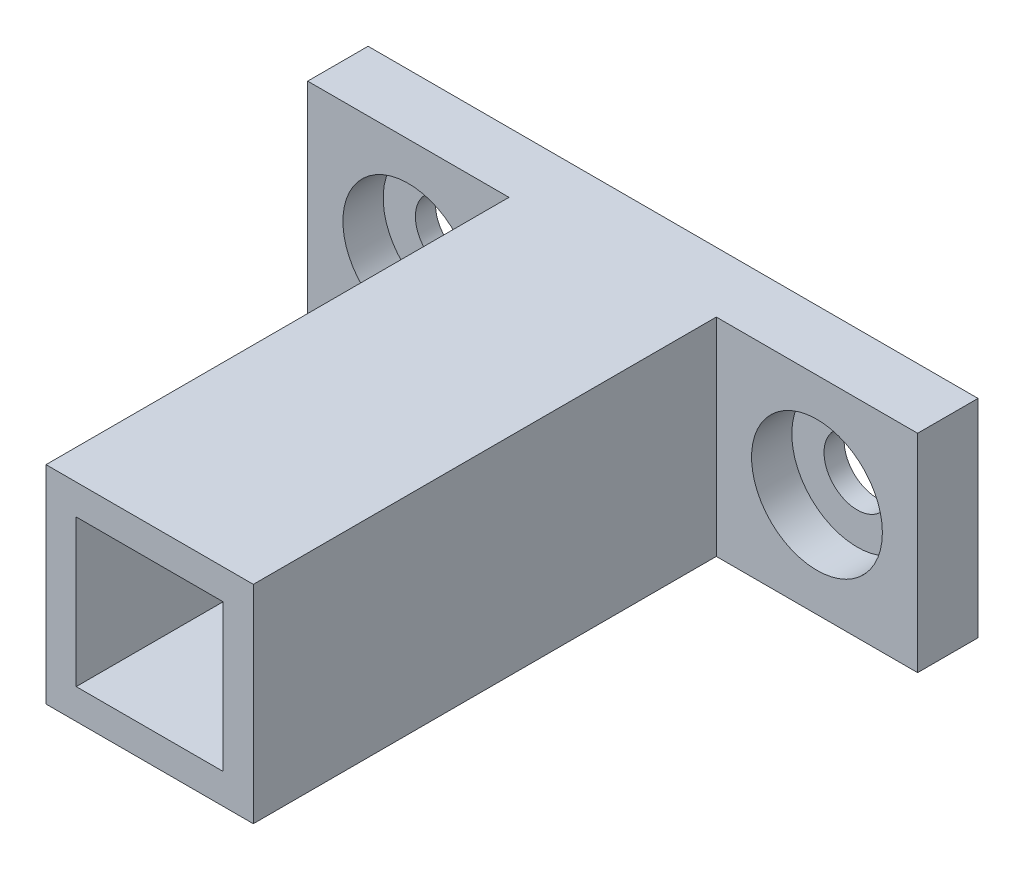
SolidWorks part; units mm, degrees
ref_plane "Alzado" through (0, 0, 0) normal (0, 0, 1) x (1, 0, 0)
ref_plane "Planta" through (0, 0, 0) normal (0, 1, 0) x (1, 0, 0)
ref_plane "Vista lateral" through (0, 0, 0) normal (1, 0, 0) x (0, 0, -1)
sketch "Croquis1" plane through (0, 0, 0) normal (0, 0, 1) x (1, 0, 0)
  line L8 (-60.1239, 65.6327) -> (-60.1239, 58.3327) construction
  line L9 (-60.1239, 65.6327) -> (-52.8239, 65.6327) construction
  line L10 (-52.8239, 65.6327) -> (-52.8239, 58.3327) construction
  line L11 (-60.1239, 58.3327) -> (-52.8239, 58.3327) construction
  line L24 (-60.1239, 65.6327) -> (-60.1239, 58.3327)
  line L25 (-60.1239, 65.6327) -> (-52.8239, 65.6327)
  line L26 (-52.8239, 65.6327) -> (-52.8239, 58.3327)
  line L27 (-60.1239, 58.3327) -> (-52.8239, 58.3327)
  line L32 (-61.6239, 67.1327) -> (-61.6239, 56.8327)
  line L33 (-61.6239, 56.8327) -> (-51.3239, 56.8327)
  line L34 (-51.3239, 67.1327) -> (-51.3239, 56.8327)
  line L35 (-61.6239, 67.1327) -> (-51.3239, 67.1327)
  dimension "D1" = 1.5
extrude "Saliente-Extruir1" add sketch "Croquis1" along normal blind 26
sketch "Croquis2" plane through (0, 0, 0) normal (0, 0, 1) x (1, 0, 0)
  line L14 (-51.3239, 67.1327) -> (-61.6239, 67.1327) construction
  line L15 (-51.3239, 67.1327) -> (-41.3239, 67.1327)
  line L16 (-51.3239, 67.1327) -> (-51.3239, 56.8327)
  line L17 (-51.3239, 56.8327) -> (-41.3239, 56.8327)
  line L18 (-41.3239, 67.1327) -> (-41.3239, 56.8327)
  line L19 (-61.6239, 56.8327) -> (-51.3239, 56.8327) construction
  line L20 (-61.6239, 67.1327) -> (-71.6239, 67.1327)
  line L21 (-61.6239, 67.1327) -> (-61.6239, 56.8327)
  line L22 (-61.6239, 56.8327) -> (-71.6239, 56.8327)
  line L23 (-71.6239, 67.1327) -> (-71.6239, 56.8327)
  line L24 (-51.3239, 56.8327) -> (-51.3239, 67.1327) construction
  line L48 (-51.3239, 67.1327) -> (-41.3239, 56.8327) construction
  line L49 (-51.3239, 56.8327) -> (-41.3239, 67.1327) construction
  line L50 (-71.6239, 67.1327) -> (-61.6239, 56.8327) construction
  line L51 (-61.6239, 67.1327) -> (-71.6239, 56.8327) construction
  line L63 (-78.2985, 7.8063) -> (69.1374, 7.8063) construction
  circle A0 centre (-66.6239, 61.9827) radius 1.65
  circle A1 centre (-46.3239, 61.9827) radius 1.65
  dimension "D8" = 3.3
  dimension "D2" = 10
  dimension "D3" = 10
extrude "Saliente-Extruir2" add sketch "Croquis2" along normal blind 3
sketch "Croquis3" plane through (0, 0, 3) normal (0, 0, 1) x (1, 0, 0)
  circle A0 centre (-66.6239, 61.9827) radius 3.25
  circle A1 centre (-46.3239, 61.9827) radius 3.25
  dimension "D1" = 6.5
extrude "Cortar-Extruir1" cut sketch "Croquis3" against normal blind 2
